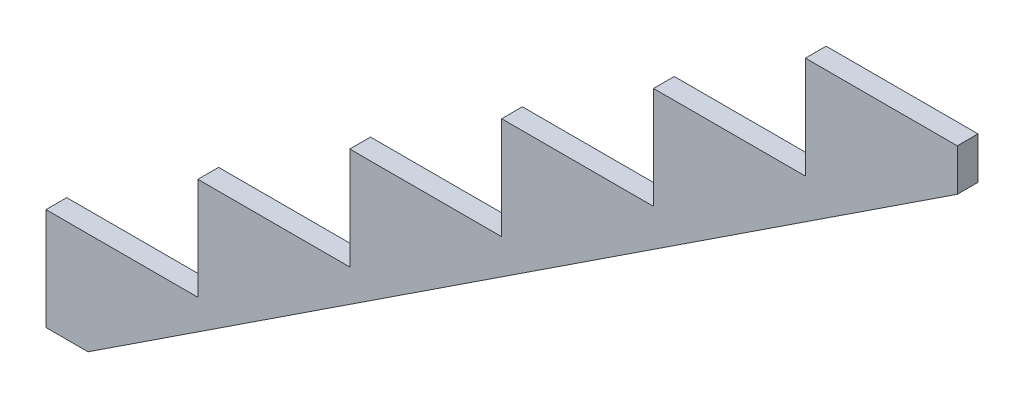
SolidWorks part; units mm, degrees
ref_plane "Front Plane" through (0, 0, 0) normal (0, 0, 1) x (1, 0, 0)
ref_plane "Top Plane" through (0, 0, 0) normal (0, 1, 0) x (1, 0, 0)
ref_plane "Right Plane" through (0, 0, 0) normal (1, 0, 0) x (0, 0, -1)
sketch "Sketch1" plane through (0, 0, 0) normal (0, 0, 1) x (1, 0, 0)
  line L0 (0, 187.96) -> (0, 0)
  line L1 (0, 187.96) -> (279.4, 187.96)
  line L2 (279.4, 187.96) -> (279.4, 375.92)
  line L3 (279.4, 375.92) -> (558.8, 375.92)
  line L4 (558.8, 375.92) -> (558.8, 563.88)
  line L5 (558.8, 563.88) -> (838.2, 563.88)
  line L6 (0, 0) -> (77.2482, 0)
  line L7 (77.2482, 0) -> (1676.4, 1050.5118)
  line L9 (279.4, 375.92) -> (390.9663, 206.0871) construction
  line L10 (1397, 939.8) -> (1397, 1127.76)
  line L11 (838.2, 563.88) -> (838.2, 751.84)
  line L12 (838.2, 751.84) -> (1117.6, 751.84)
  line L13 (1117.6, 751.84) -> (1117.6, 939.8)
  line L14 (1117.6, 939.8) -> (1397, 939.8)
  line L16 (1397, 1127.76) -> (1676.4, 1127.76)
  line L17 (1676.4, 1127.76) -> (1676.4, 1050.5118)
  point P10 (1789.2448, 1078.123)
  dimension "D1" = 279.4
  dimension "D2" = 187.96
  dimension "D3" = 203.2
extrude "Boss-Extrude1" add sketch "Sketch1" along normal blind 38.1
